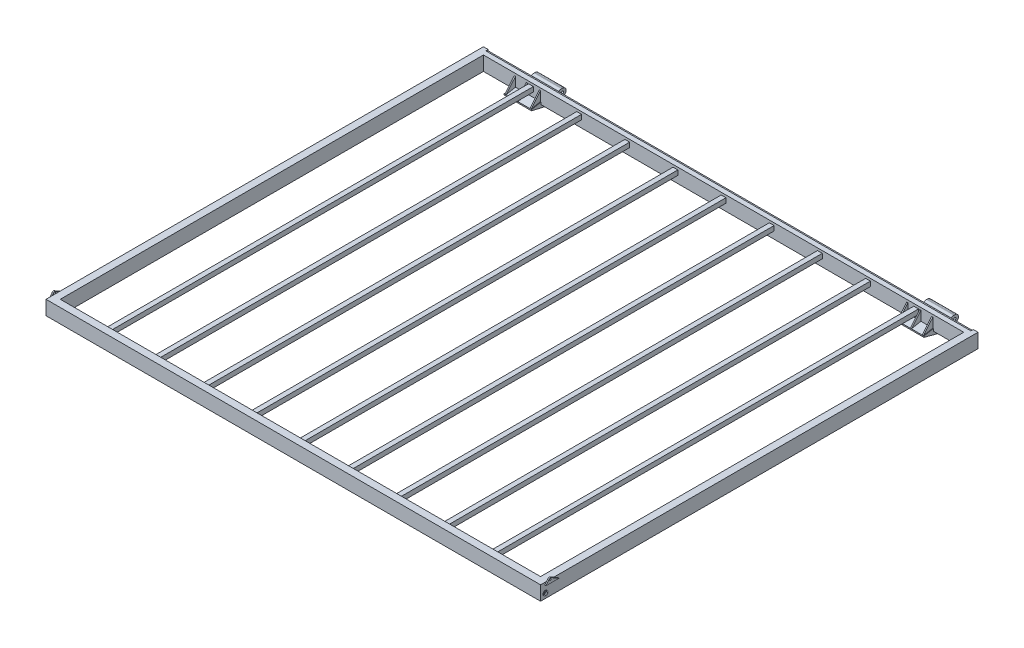
SolidWorks part; units mm, degrees
material "6063-T6"
ref_plane "Front Plane" through (0, 0, 0) normal (0, 0, 1) x (1, 0, 0)
ref_plane "Top Plane" through (0, 0, 0) normal (0, 1, 0) x (1, 0, 0)
ref_plane "Right Plane" through (0, 0, 0) normal (1, 0, 0) x (0, 0, -1)
sketch "Sketch1" plane through (0, 0, 0) normal (1, 0, 0) x (0, 0, -1)
  line L7 (1130.173, 38.1) -> (1168.273, 38.1)
  line L8 (1130.173, 38.1) -> (1130.173, -38.1)
  line L9 (1130.173, -38.1) -> (1168.273, -38.1)
  line L10 (1168.273, 38.1) -> (1168.273, -38.1)
  line L11 (1130.173, 38.1) -> (1168.273, -38.1) construction
  line L12 (1130.173, -38.1) -> (1168.273, 38.1) construction
  line L17 (1133.348, 34.925) -> (1133.348, -34.925)
  line L18 (1133.348, -34.925) -> (1165.098, -34.925)
  line L19 (1165.098, 34.925) -> (1165.098, -34.925)
  line L20 (1133.348, 34.925) -> (1165.098, 34.925)
  point P5 (1149.223, 0)
  dimension "D1" = 76.2
  dimension "D2" = 38.1
  dimension "D3" = 1149.223
  dimension "D6" = 3.175
sketch "Sketch2" plane through (0, 0, 0) normal (0, 1, 0) x (1, 0, 0)
  line L1 (1301.75, 1149.223) -> (-1301.75, 1149.223)
  line L2 (1301.75, 1149.223) -> (1301.75, -1149.223)
  line L3 (1301.75, -1149.223) -> (-1301.75, -1149.223)
  line L4 (-1301.75, 1149.223) -> (-1301.75, -1149.223)
  line L5 (1301.75, 1149.223) -> (-1301.75, -1149.223) construction
  line L6 (1301.75, -1149.223) -> (-1301.75, 1149.223) construction
  point P0 (0, 0)
  dimension "D1" = 2603.5
sweep "FLOOR FRAM" add profiles "Sketch1" path "Sketch2"
ref_plane "RS PIN PLANE" through (-1120.775, 0, 0) normal (1, 0, 0) x (0, 0, -1)
ref_plane "LS PIN PLANE" through (1120.775, 0, 0) normal (1, 0, 0) x (0, 0, -1)
sketch "Sketch3" plane through (1120.775, 0, 0) normal (1, 0, 0) x (0, 0, -1)
  line L0 (1168.273, 38.1) -> (1168.273, -38.1) construction
  circle A0 centre (1244.727, -38.1) radius 6.35
  point P4 (1168.273, 0)
  dimension "D1" = 12.7
  dimension "D2" = 76.454
  dimension "D3" = 38.1
sketch "Sketch4" plane through (1120.775, 0, 0) normal (1, 0, 0) x (0, 0, -1)
  line L0 (1168.273, -38.1) -> (1168.4722, -38.2992)
  line L1 (-1168.273, -38.1) -> (1168.273, -38.1) construction
  line L2 (1175.6564, -41.275) -> (1181.9096, -41.275)
  line L3 (1186.1791, -40.3344) -> (1224.523, -22.5773)
  line L4 (1240.5336, -19.05) -> (1244.8398, -19.05)
  line L7 (1252.7131, -55.2707) -> (1238.9524, -60.775)
  line L8 (1224.8024, -63.5) -> (1167.3074, -63.5)
  line L9 (1157.4433, -62.2009) -> (1079.373, -41.275)
  line L10 (1079.373, -41.275) -> (1079.373, -34.925)
  line L11 (1079.373, -34.925) -> (1130.173, -25.4)
  line L12 (1130.173, -25.4) -> (1130.173, -38.1)
  line L13 (1130.173, -38.1) -> (1168.273, -38.1)
  line L14 (1263.8898, -38.7624) -> (1263.8898, -38.1)
  line L15 (1168.273, 38.1) -> (1168.273, -38.1) construction
  arc A0 (1240.5336, -19.05) -> (1224.523, -22.5773) centre (1240.5336, -57.15) ccw
  arc A1 (1157.4433, -62.2009) -> (1167.3074, -63.5) centre (1167.3074, -25.4) ccw
  arc A2 (1224.8024, -63.5) -> (1238.9524, -60.775) centre (1224.8024, -25.4) ccw
  arc A3 (1186.1791, -40.3344) -> (1181.9096, -41.275) centre (1181.9096, -31.115) cw
  arc A4 (1175.6564, -41.275) -> (1168.4722, -38.2992) centre (1175.6564, -31.115) cw
  arc A5 (1244.8398, -19.05) -> (1263.8898, -38.1) centre (1244.8398, -38.1) cw
  arc A6 (1263.8898, -38.7624) -> (1252.7131, -55.2707) centre (1246.1098, -38.7624) cw
  point P25 (1079.373, -38.1)
  point P32 (1232.1398, -19.05)
  point P35 (1162.2898, -63.5)
  point P38 (1232.1398, -63.5)
  point P42 (1184.148, -41.275)
  point P45 (1171.448, -41.275)
  point P48 (1263.8898, -19.05)
  point P51 (1263.8898, -50.8)
  dimension "D14" = 38.1
  dimension "D15" = 10.16
  dimension "D16" = 19.05
  dimension "D17" = 17.78
  dimension "D1" = 44.45
  dimension "D2" = 12.7
  dimension "D3" = 50.8
  dimension "D4" = 6.35
  dimension "D5" = 12.7
  dimension "D6" = 25.4
  dimension "D7" = 19.1628
  dimension "D8" = 3.175
  dimension "D9" = 3.175
  dimension "D10" = 69.85
  dimension "D11" = 31.75
  dimension "D12" = 31.75
  dimension "D13" = 12.7
extrude "LS PIN HOUSING" add sketch "Sketch4" against normal blind 146.05
sketch "Sketch6" plane through (-1120.775, 0, 0) normal (1, 0, 0) x (0, 0, -1)
  line L0 (1168.273, -38.1) -> (1178.3745, -40.9047)
  line L1 (1079.373, -34.925) -> (1079.373, -41.275) construction
  line L2 (1181.0926, -41.275) -> (1181.9096, -41.275)
  line L3 (1186.1791, -40.3344) -> (1224.523, -22.5773)
  line L4 (1240.5336, -19.05) -> (1244.8398, -19.05)
  line L7 (1252.7131, -55.2707) -> (1238.9524, -60.775)
  line L8 (1224.8024, -63.5) -> (1183.7995, -63.5)
  line L9 (1175.5535, -62.5969) -> (1079.373, -41.275)
  line L10 (1079.373, -41.275) -> (1079.373, -34.925)
  line L11 (1079.373, -34.925) -> (1130.173, -25.4)
  line L12 (1130.173, -25.4) -> (1130.173, -38.1)
  line L13 (1130.173, -38.1) -> (1168.273, -38.1)
  line L14 (1263.8898, -38.7624) -> (1263.8898, -38.1)
  line L15 (1168.273, 38.1) -> (1168.273, -38.1) construction
  line L16 (1238.9524, -60.775) -> (1252.7131, -55.2707) construction
  line L17 (-1168.273, -38.1) -> (1168.273, -38.1) construction
  arc A0 (1240.5336, -19.05) -> (1224.523, -22.5773) centre (1240.5336, -57.15) ccw
  arc A1 (1175.5535, -62.5969) -> (1183.7995, -63.5) centre (1183.7995, -25.4) ccw
  arc A2 (1224.8024, -63.5) -> (1238.9524, -60.775) centre (1224.8024, -25.4) ccw
  arc A3 (1186.1791, -40.3344) -> (1181.9096, -41.275) centre (1181.9096, -31.115) cw
  arc A4 (1181.0926, -41.275) -> (1178.3745, -40.9047) centre (1181.0926, -31.115) cw
  arc A5 (1244.8398, -19.05) -> (1263.8898, -38.1) centre (1244.8398, -38.1) cw
  arc A6 (1263.8898, -38.7624) -> (1252.7131, -55.2707) centre (1246.1098, -38.7624) cw
  arc A7 (1224.8024, -63.5) -> (1238.9524, -60.775) centre (1224.8024, -25.4) ccw construction
  arc A8 (1263.8898, -38.1) -> (1244.8398, -19.05) centre (1244.8398, -38.1) ccw construction
  arc A9 (1168.4722, -38.2992) -> (1175.6564, -41.275) centre (1175.6564, -31.115) ccw construction
  arc A10 (1157.4433, -62.2009) -> (1167.3074, -63.5) centre (1167.3074, -25.4) ccw construction
  point P30 (1079.373, -38.1)
  dimension "D14" = 38.1
  dimension "D15" = 10.16
  dimension "D16" = 19.05
  dimension "D17" = 17.78
  dimension "D1" = 44.45
  dimension "D3" = 50.8
  dimension "D4" = 6.35
  dimension "D5" = 12.7
  dimension "D6" = 25.4
  dimension "D8" = 3.175
extrude "RS PIN HOUSING" add sketch "Sketch6" along normal blind 146.05
sketch "Sketch9" plane through (1320.8, 0, 0) normal (1, 0, 0) x (0, 0, -1)
  line L0 (-1168.273, -38.1) -> (1168.273, -38.1) construction
  line L1 (-1168.273, 38.1) -> (-1168.273, -38.1) construction
  circle A0 centre (-1142.873, -12.7) radius 12.7
  dimension "D1" = 25.4
  dimension "D2" = 25.4
  dimension "D3" = 25.4
extrude "LS CABLE SUPPORT" add sketch "Sketch9" along normal mid plane 6.35 contours A0
sketch "Sketch11" plane through (-1320.8, 0, 0) normal (-1, 0, 0) x (0, 0, 1)
  line L0 (1168.273, 38.1) -> (1168.273, -38.1) construction
  line L1 (-1168.273, -38.1) -> (1168.273, -38.1) construction
  circle A0 centre (1142.873, -12.7) radius 12.7
  dimension "D1" = 25.4
  dimension "D3" = 25.4
  dimension "D2" = 25.4
extrude "RS CABLE SUPPORT" add sketch "Sketch11" along normal mid plane 6.35
extrude "CANTILVER PIN" cut sketch "Sketch3" against normal up to surface (2241.55 mm away) up to face at (-1120.775, -41.2049, -1191.3077)
sketch "Sketch7" plane through (0, -229.2479, -42.984) normal (0, 0.9829, 0.1843) x (1, 0, 0)
  line L0 (-1054.1, 1106.1347) -> (-1047.75, 1106.1347)
  line L1 (-1117.6, 1106.1347) -> (-1111.25, 1106.1347)
  line L2 (-1117.6, 1106.1347) -> (-1117.6, 1055.3347)
  line L3 (-1117.6, 1055.3347) -> (-1111.25, 1055.3347)
  line L4 (-1111.25, 1106.1347) -> (-1111.25, 1055.3347)
  line L5 (-1117.6, 1106.1347) -> (-1111.25, 1055.3347) construction
  line L6 (-1117.6, 1055.3347) -> (-1111.25, 1106.1347) construction
  line L7 (-1054.1, 1106.1347) -> (-1054.1, 1055.3347)
  line L9 (-1120.775, 1106.1347) -> (-1120.775, 1054.4494) construction
  line L10 (-1054.1, 1055.3347) -> (-1047.75, 1055.3347)
  line L11 (-1047.75, 1106.1347) -> (-1047.75, 1055.3347)
  line L12 (-1054.1, 1106.1347) -> (-1047.75, 1055.3347) construction
  line L13 (-1054.1, 1055.3347) -> (-1047.75, 1106.1347) construction
  line L14 (-984.25, 1106.1347) -> (-977.9, 1106.1347)
  line L15 (-984.25, 1106.1347) -> (-984.25, 1055.3347)
  line L16 (-984.25, 1055.3347) -> (-977.9, 1055.3347)
  line L17 (-977.9, 1106.1347) -> (-977.9, 1055.3347)
  line L18 (-984.25, 1106.1347) -> (-977.9, 1055.3347) construction
  line L19 (-984.25, 1055.3347) -> (-977.9, 1106.1347) construction
  line L20 (-974.725, 1106.1347) -> (-974.725, 1054.4494) construction
  line L21 (1047.75, 1106.1347) -> (1054.1, 1106.1347)
  line L22 (977.9, 1106.1347) -> (984.25, 1106.1347)
  line L23 (977.9, 1106.1347) -> (977.9, 1055.3347)
  line L24 (977.9, 1055.3347) -> (984.25, 1055.3347)
  line L25 (984.25, 1106.1347) -> (984.25, 1055.3347)
  line L26 (977.9, 1106.1347) -> (984.25, 1055.3347) construction
  line L27 (977.9, 1055.3347) -> (984.25, 1106.1347) construction
  line L28 (1047.75, 1106.1347) -> (1047.75, 1055.3347)
  line L29 (1047.75, 1055.3347) -> (1054.1, 1055.3347)
  line L30 (1054.1, 1106.1347) -> (1054.1, 1055.3347)
  line L31 (1047.75, 1106.1347) -> (1054.1, 1055.3347) construction
  line L32 (1047.75, 1055.3347) -> (1054.1, 1106.1347) construction
  line L33 (1111.25, 1106.1347) -> (1117.6, 1106.1347)
  line L34 (1111.25, 1106.1347) -> (1111.25, 1055.3347)
  line L35 (1111.25, 1055.3347) -> (1117.6, 1055.3347)
  line L36 (1117.6, 1106.1347) -> (1117.6, 1055.3347)
  line L37 (1111.25, 1106.1347) -> (1117.6, 1055.3347) construction
  line L38 (1111.25, 1055.3347) -> (1117.6, 1106.1347) construction
  line L39 (974.725, 1106.1347) -> (1120.775, 1106.1347) construction
  line L40 (1120.775, 1106.1347) -> (1120.775, 1054.4494) construction
  line L41 (974.725, 1106.1347) -> (974.725, 1054.4494) construction
  line L42 (-974.725, 1106.1347) -> (-1120.775, 1106.1347) construction
  point P0 (-1114.425, 1080.7347)
  point P12 (-1050.925, 1080.7347)
  point P17 (-981.075, 1080.7347)
  point P24 (981.075, 1080.7347)
  point P29 (1050.925, 1080.7347)
  point P34 (1114.425, 1080.7347)
  dimension "D1" = 6.35
  dimension "D2" = 50.8
  dimension "D3" = 6.35
  dimension "D4" = 6.35
  dimension "D5" = 6.35
  dimension "D6" = 6.35
  dimension "D7" = 76.2
  dimension "D8" = 6.35
  dimension "D9" = 6.35
  dimension "D10" = 6.35
  dimension "D11" = 6.35
  dimension "D12" = 76.2
  dimension "D13" = 6.35
revolve "FLANGE SUPPORT" add sketch "Sketch7" angle 100.62 about axis through (-974.725, -25.4, -1130.173) along (-1, 0, 0)
sketch "Sketch8" plane through (1117.6, 0, 0) normal (1, 0, 0) x (0, 0, -1)
  line L0 (1080.2431, -34.7619) -> (1130.173, 25.4)
  arc A0 (1130.173, 25.4) -> (1080.2431, -34.7619) centre (1127.8868, -23.5026) ccw
extrude "Cut-Extrude2" cut sketch "Sketch8" against normal up to surface (2235.2 mm away) up to face at (-1117.6, -7.6794, -1108.821)
sketch "Sketch12" plane through (-1323.975, 0, 0) normal (-1, 0, 0) x (0, 0, 1)
  circle A0 centre (1142.873, -12.7) radius 7.9375
  dimension "D1" = 15.875
extrude "RS BOLT HOLE" cut sketch "Sketch12" against normal blind 9.525
sketch "Sketch10" plane through (1323.975, 0, 0) normal (1, 0, 0) x (0, 0, -1)
  circle A0 centre (-1142.873, -12.7) radius 7.9375
  dimension "D1" = 15.875
extrude "LS BOLT HOLE" cut sketch "Sketch10" against normal blind 9.525 contours A0
sketch "Sketch15" plane through (1320.8, 0, 0) normal (1, 0, 0) x (0, 0, -1)
  line L0 (-1168.273, 38.1) -> (1168.273, 38.1) construction
  line L1 (-1168.273, 38.1) -> (-1168.273, -38.1) construction
  line L2 (-1128.4772, 47.766) -> (-1146.048, 25.4)
  line L3 (-1146.048, 25.4) -> (-1076.198, 25.4)
  line L4 (-1076.198, 25.4) -> (-1117.5838, 49.2941)
  arc A0 (-1117.5838, 49.2941) -> (-1128.4772, 47.766) centre (-1122.2355, 42.8625) ccw
  dimension "D1" = 15.875
  dimension "D2" = 4.7625
  dimension "D3" = 46.0375
  dimension "D4" = 69.85
  dimension "D5" = 12.7
  dimension "D6" = 30
  dimension "D7" = 22.225
extrude "LS FARWALL PIN SUPPORT" add sketch "Sketch15" along normal blind 6.35
sketch "Sketch16" plane through (-1320.8, 0, 0) normal (-1, 0, 0) x (0, 0, 1)
  line L0 (1168.273, 38.1) -> (1168.273, -38.1) construction
  line L2 (-1168.273, 38.1) -> (1168.273, 38.1) construction
  line L3 (1128.5022, 47.7341) -> (1145.921, 25.3267)
  line L4 (1145.921, 25.3267) -> (1076.071, 25.3267)
  line L5 (1076.071, 25.3267) -> (1117.5838, 49.2941)
  arc A0 (1128.5022, 47.7341) -> (1117.5838, 49.2941) centre (1122.2355, 42.8625) ccw
  dimension "D6" = 15.875
  dimension "D2" = 4.7625
  dimension "D3" = 69.85
  dimension "D4" = 22.352
  dimension "D5" = 30
extrude "RS FARWALL PIN SUPPORT" add sketch "Sketch16" along normal blind 6.35
sketch "Sketch14" plane through (1327.15, 0, 0) normal (1, 0, 0) x (0, 0, -1)
  line L0 (-1168.273, 38.1) -> (-1168.273, -38.1) construction
  line L1 (-2384.3544, 38.1) -> (2479.9712, 38.1) construction
  circle A0 centre (-1122.2355, 42.8625) radius 4.7625
  dimension "D3" = 9.525
  dimension "D1" = 46.0375
  dimension "D2" = 4.7625
extrude "FARWALL PIN HOLE" cut sketch "Sketch14" against normal up to surface (2654.3 mm away) up to face at (-1327.15, 37.4719, 1117.0983)
sketch "Sketch17" plane through (0, 0, -1130.173) normal (0, 0, 1) x (1, 0, 0)
  line L0 (-1282.7, -38.1) -> (-1282.7, 38.1) construction
  line L1 (-1041.4, 25.4) -> (-1016, 25.4)
  line L2 (-1041.4, 25.4) -> (-1041.4, 0)
  line L3 (-1041.4, 0) -> (-1016, 0)
  line L4 (-1016, 25.4) -> (-1016, 0)
  line L5 (-1041.4, 25.4) -> (-1016, 0) construction
  line L6 (-1041.4, 0) -> (-1016, 25.4) construction
  line L7 (1282.7, 38.1) -> (-1282.7, 38.1) construction
  line L44 (-1038.225, 22.225) -> (-1038.225, 3.175)
  line L45 (-1038.225, 3.175) -> (-1019.175, 3.175)
  line L46 (-1019.175, 22.225) -> (-1019.175, 3.175)
  line L47 (-1038.225, 22.225) -> (-1019.175, 22.225)
  line L48 (-781.05, 22.225) -> (-781.05, 3.175)
  line L49 (-781.05, 3.175) -> (-762, 3.175)
  line L50 (-762, 22.225) -> (-762, 3.175)
  line L51 (-781.05, 22.225) -> (-762, 22.225)
  line L52 (-784.225, 25.4) -> (-784.225, 0)
  line L53 (-784.225, 25.4) -> (-758.825, 25.4)
  line L54 (-758.825, 25.4) -> (-758.825, 0)
  line L55 (-784.225, 0) -> (-758.825, 0)
  line L56 (-523.875, 22.225) -> (-523.875, 3.175)
  line L57 (-523.875, 3.175) -> (-504.825, 3.175)
  line L58 (-504.825, 22.225) -> (-504.825, 3.175)
  line L59 (-523.875, 22.225) -> (-504.825, 22.225)
  line L60 (-527.05, 25.4) -> (-527.05, 0)
  line L61 (-527.05, 25.4) -> (-501.65, 25.4)
  line L62 (-501.65, 25.4) -> (-501.65, 0)
  line L63 (-527.05, 0) -> (-501.65, 0)
  line L64 (-266.7, 22.225) -> (-266.7, 3.175)
  line L65 (-266.7, 3.175) -> (-247.65, 3.175)
  line L66 (-247.65, 22.225) -> (-247.65, 3.175)
  line L67 (-266.7, 22.225) -> (-247.65, 22.225)
  line L68 (-269.875, 25.4) -> (-269.875, 0)
  line L69 (-269.875, 25.4) -> (-244.475, 25.4)
  line L70 (-244.475, 25.4) -> (-244.475, 0)
  line L71 (-269.875, 0) -> (-244.475, 0)
  line L72 (-9.525, 22.225) -> (-9.525, 3.175)
  line L73 (-9.525, 3.175) -> (9.525, 3.175)
  line L74 (9.525, 22.225) -> (9.525, 3.175)
  line L75 (-9.525, 22.225) -> (9.525, 22.225)
  line L76 (-12.7, 25.4) -> (-12.7, 0)
  line L77 (-12.7, 25.4) -> (12.7, 25.4)
  line L78 (12.7, 25.4) -> (12.7, 0)
  line L79 (-12.7, 0) -> (12.7, 0)
  line L80 (247.65, 22.225) -> (247.65, 3.175)
  line L81 (247.65, 3.175) -> (266.7, 3.175)
  line L82 (266.7, 22.225) -> (266.7, 3.175)
  line L83 (247.65, 22.225) -> (266.7, 22.225)
  line L84 (244.475, 25.4) -> (244.475, 0)
  line L85 (244.475, 25.4) -> (269.875, 25.4)
  line L86 (269.875, 25.4) -> (269.875, 0)
  line L87 (244.475, 0) -> (269.875, 0)
  line L88 (504.825, 22.225) -> (504.825, 3.175)
  line L89 (504.825, 3.175) -> (523.875, 3.175)
  line L90 (523.875, 22.225) -> (523.875, 3.175)
  line L91 (504.825, 22.225) -> (523.875, 22.225)
  line L92 (501.65, 25.4) -> (501.65, 0)
  line L93 (501.65, 25.4) -> (527.05, 25.4)
  line L94 (527.05, 25.4) -> (527.05, 0)
  line L95 (501.65, 0) -> (527.05, 0)
  line L96 (762, 22.225) -> (762, 3.175)
  line L97 (762, 3.175) -> (781.05, 3.175)
  line L98 (781.05, 22.225) -> (781.05, 3.175)
  line L99 (762, 22.225) -> (781.05, 22.225)
  line L100 (758.825, 25.4) -> (758.825, 0)
  line L101 (758.825, 25.4) -> (784.225, 25.4)
  line L102 (784.225, 25.4) -> (784.225, 0)
  line L103 (758.825, 0) -> (784.225, 0)
  line L104 (1019.175, 22.225) -> (1019.175, 3.175)
  line L105 (1019.175, 3.175) -> (1038.225, 3.175)
  line L106 (1038.225, 22.225) -> (1038.225, 3.175)
  line L107 (1019.175, 22.225) -> (1038.225, 22.225)
  line L108 (1016, 25.4) -> (1016, 0)
  line L109 (1016, 25.4) -> (1041.4, 25.4)
  line L110 (1041.4, 25.4) -> (1041.4, 0)
  line L111 (1016, 0) -> (1041.4, 0)
  line L112 (1282.7, -38.1) -> (1282.7, 38.1) construction
  point P0 (-1028.7, 12.7)
  point P13 (1028.7, 25.4)
  dimension "D1" = 254
  dimension "D2" = 25.4
  dimension "D3" = 25.4
  dimension "D4" = 12.7
  dimension "D7" = 254
  dimension "D5" = 3.175
  dimension "D6" = 9
extrude "CROSS SUPPORTS" add sketch "Sketch17" along normal up to surface (2260.346 mm away) up to face at (0, 0, 1130.173)
sketch "Sketch18" plane through (0, 0, -1168.273) normal (0, 0, -1) x (-1, 0, 0)
  line L0 (-1320.8, 38.1) -> (1320.8, 38.1) construction
  line L1 (-1301.75, 38.1) -> (1301.75, 38.1)
  line L2 (-1301.75, 38.1) -> (-1301.75, 25.4)
  line L3 (-1301.75, 25.4) -> (1301.75, 25.4)
  line L4 (1301.75, 38.1) -> (1301.75, 25.4)
  line L5 (-1301.75, 38.1) -> (1301.75, 25.4) construction
  line L6 (-1301.75, 25.4) -> (1301.75, 38.1) construction
  point P0 (0, 31.75)
  dimension "D1" = 12.7
  dimension "D2" = 2603.5
extrude "Boss-Extrude1" add sketch "Sketch18" against normal blind 19.05
sketch "Sketch19" plane through (0, 0, -1168.273) normal (0, 0, -1) x (-1, 0, 0)
  line L0 (-1320.8, 38.1) -> (1320.8, 38.1) construction
  line L1 (-1295.4, 38.1) -> (1295.4, 38.1)
  line L2 (-1295.4, 38.1) -> (-1295.4, 31.75)
  line L3 (-1295.4, 31.75) -> (1295.4, 31.75)
  line L4 (1295.4, 38.1) -> (1295.4, 31.75)
  line L5 (-1295.4, 38.1) -> (1295.4, 31.75) construction
  line L6 (-1295.4, 31.75) -> (1295.4, 38.1) construction
  point P0 (0, 34.925)
  dimension "D1" = 2590.8
  dimension "D2" = 6.35
extrude "Cut-Extrude4" cut sketch "Sketch19" against normal blind 12.7
